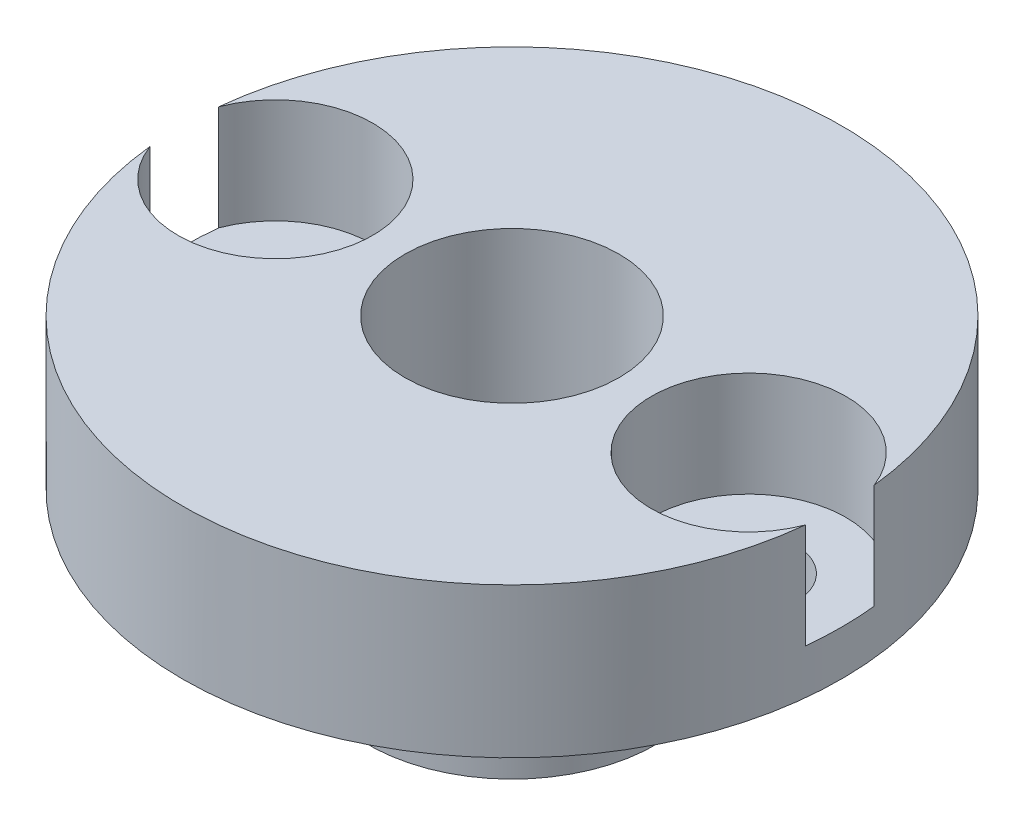
SolidWorks part; units mm, degrees
ref_plane "Alzado" through (0, 0, 0) normal (0, 0, 1) x (1, 0, 0)
ref_plane "Planta" through (0, 0, 0) normal (0, 1, 0) x (1, 0, 0)
ref_plane "Vista lateral" through (0, 0, 0) normal (1, 0, 0) x (0, 0, -1)
sketch "Croquis1" plane through (0, 0, 0) normal (0, 1, 0) x (1, 0, 0)
  circle A0 centre (0, 0) radius 11
  dimension "D1" = 22
extrude "Saliente-Extruir1" add sketch "Croquis1" along normal blind 5
sketch "Croquis2" plane through (0, 0, 0) normal (0, -1, 0) x (1, 0, 0)
  circle A0 centre (0, 0) radius 4.8
  dimension "D1" = 9.6
extrude "Saliente-Extruir2" add sketch "Croquis2" along normal blind 5
sketch "Croquis3" plane through (0, 0, 0) normal (0, -1, 0) x (1, 0, 0)
  line L0 (0, 0) -> (0, 5.9276) construction
  line L1 (-4.8, 0) -> (-11, 0) construction
  circle A0 centre (-7.9, 0) radius 1.6
  circle A1 centre (7.9, 0) radius 1.6
  circle A2 centre (0, 0) radius 4.8 construction
  circle A3 centre (0, 0) radius 4.8 construction
  circle A4 centre (0, 0) radius 11 construction
  dimension "D1" = 3.2
extrude "Cortar-Extruir1" cut sketch "Croquis3" against normal through all
sketch "Croquis4" plane through (0, -5, 0) normal (0, -1, 0) x (1, 0, 0)
  circle A1 centre (0, 0) radius 3.575
  dimension "D1" = 7.15
extrude "Cortar-Extruir2" cut sketch "Croquis4" against normal through all
sketch "Croquis5" plane through (0, 5, 0) normal (0, 1, 0) x (1, 0, 0)
  circle A0 centre (-7.9, 0) radius 3.25
  circle A1 centre (7.9, 0) radius 3.25
  dimension "D1" = 6.5
extrude "Cortar-Extruir3" cut sketch "Croquis5" against normal blind 3.5
